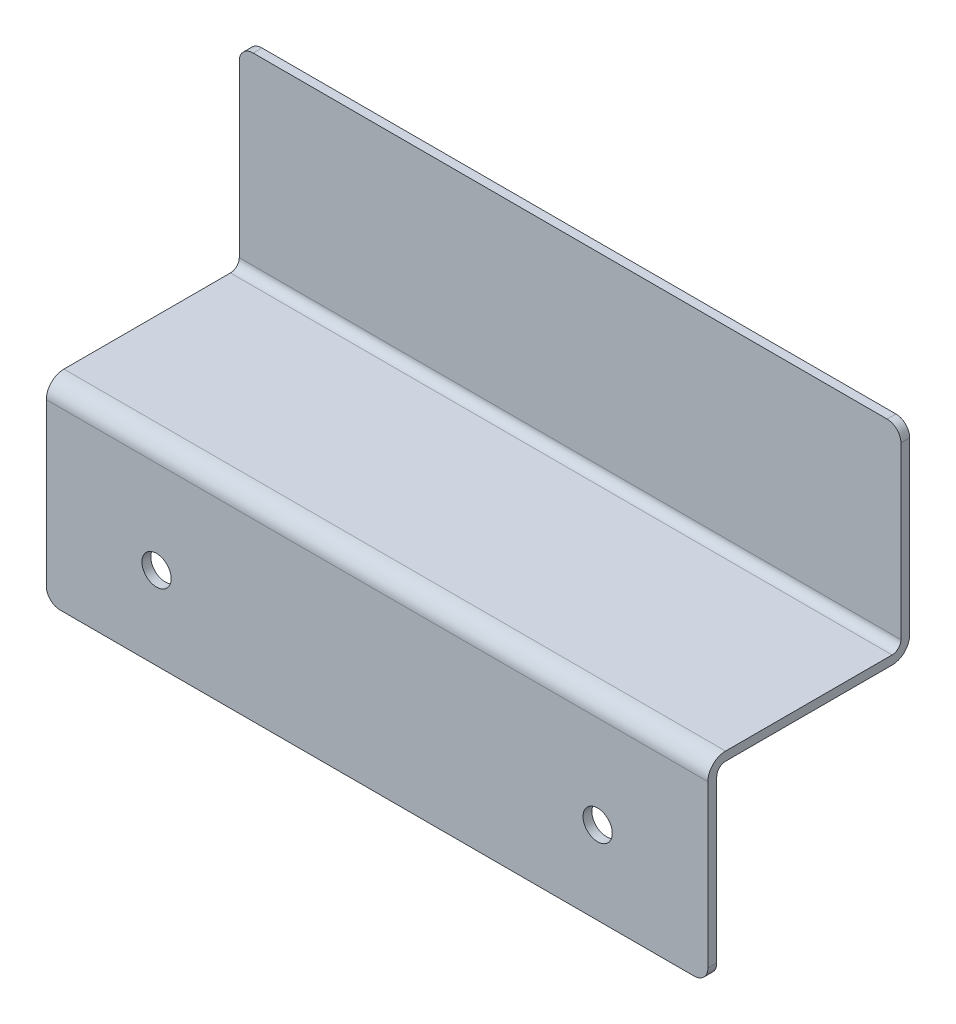
SolidWorks part; units mm, degrees
material "5052-H32"
ref_plane "Front Plane" through (0, 0, 0) normal (0, 0, 1) x (1, 0, 0)
ref_plane "Top Plane" through (0, 0, 0) normal (0, 1, 0) x (1, 0, 0)
ref_plane "Right Plane" through (0, 0, 0) normal (1, 0, 0) x (0, 0, -1)
sketch "Sketch1" plane through (0, 0, 0) normal (1, 0, 0) x (0, 0, -1)
  line L0 (0, 0) -> (0, -44.45)
  line L1 (0, -44.45) -> (-44.45, -44.45)
  line L2 (-44.45, -44.45) -> (-44.45, -88.9)
  line L3 (2.032, 0) -> (2.032, -46.482)
  line L4 (2.032, -46.482) -> (-42.418, -46.482)
  line L5 (-42.418, -46.482) -> (-42.418, -88.9)
  line L6 (-44.45, -88.9) -> (-42.418, -88.9)
  line L7 (0, 0) -> (2.032, 0)
  dimension "D1" = 2.032
  dimension "D2" = 44.45
  dimension "D3" = 88.9
  dimension "D4" = 44.45
extrude "Boss-Extrude1" add sketch "Sketch1" along normal blind 152.4
fillet "Fillet1" radius 2.032 2 edges at (76.2, -46.482, 42.418) (76.2, -44.45, 0)
fillet "Fillet2" radius 4.064 2 edges at (76.2, -44.45, 44.45) (76.2, -46.482, -2.032)
fillet "Fillet3" radius 3.175 4 edges at (0, -88.9, 43.434) (0, 0, -1.016) (152.4, -88.9, 43.434) (152.4, 0, -1.016)
sketch "Sketch2" plane through (0, 0, 44.45) normal (0, 0, 1) x (1, 0, 0)
  line L0 (149.225, -88.9) -> (3.175, -88.9) construction
  line L1 (0, -48.514) -> (0, -85.725) construction
  circle A0 centre (25.4, -69.85) radius 3.3655
  circle A1 centre (127, -69.85) radius 3.3655
  dimension "D1" = 19.05
  dimension "D4" = 6.731
  dimension "D2" = 25.4
  dimension "D3" = 127
extrude "Cut-Extrude1" cut sketch "Sketch2" against normal through all
